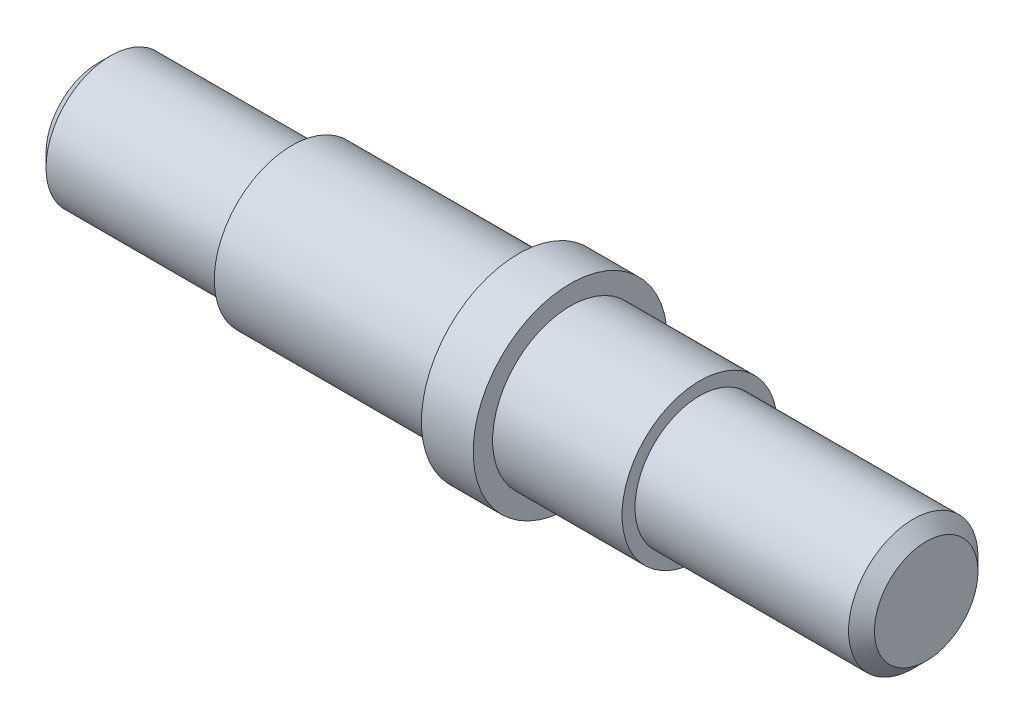
SolidWorks part; units mm, degrees
ref_plane "Přední rovina" through (0, 0, 0) normal (0, 0, 1) x (1, 0, 0)
ref_plane "Vrchní rovina" through (0, 0, 0) normal (0, 1, 0) x (1, 0, 0)
ref_plane "Pravá rovina" through (0, 0, 0) normal (1, 0, 0) x (0, 0, -1)
sketch "Skica1" plane through (0, 0, 0) normal (0, 0, 1) x (1, 0, 0)
  line L0 (0, 0) -> (0, 10)
  line L1 (0, 10) -> (30, 10)
  line L2 (30, 10) -> (30, 12)
  line L3 (30, 12) -> (65, 12)
  line L4 (65, 12) -> (65, 15)
  line L5 (65, 15) -> (73, 15)
  line L6 (73, 15) -> (73, 12)
  line L7 (73, 12) -> (93, 12)
  line L8 (93, 12) -> (93, 10)
  line L9 (93, 10) -> (128, 10)
  line L10 (128, 10) -> (128, 0)
  line L11 (128, 0) -> (0, 0) construction
  line L12 (0, 0) -> (128, 0)
  dimension "D1" = 30
  dimension "D2" = 65
  dimension "D3" = 8
  dimension "D4" = 20
  dimension "D5" = 55
  dimension "D6" = 20
  dimension "D7" = 24
  dimension "D8" = 30
revolve "Rotovat1" add sketch "Skica1" angle 360 about L11
chamfer "Zkosení1" distance 2 angle 45 2 edges at (0, 0, -10) (128, 0, -10)
